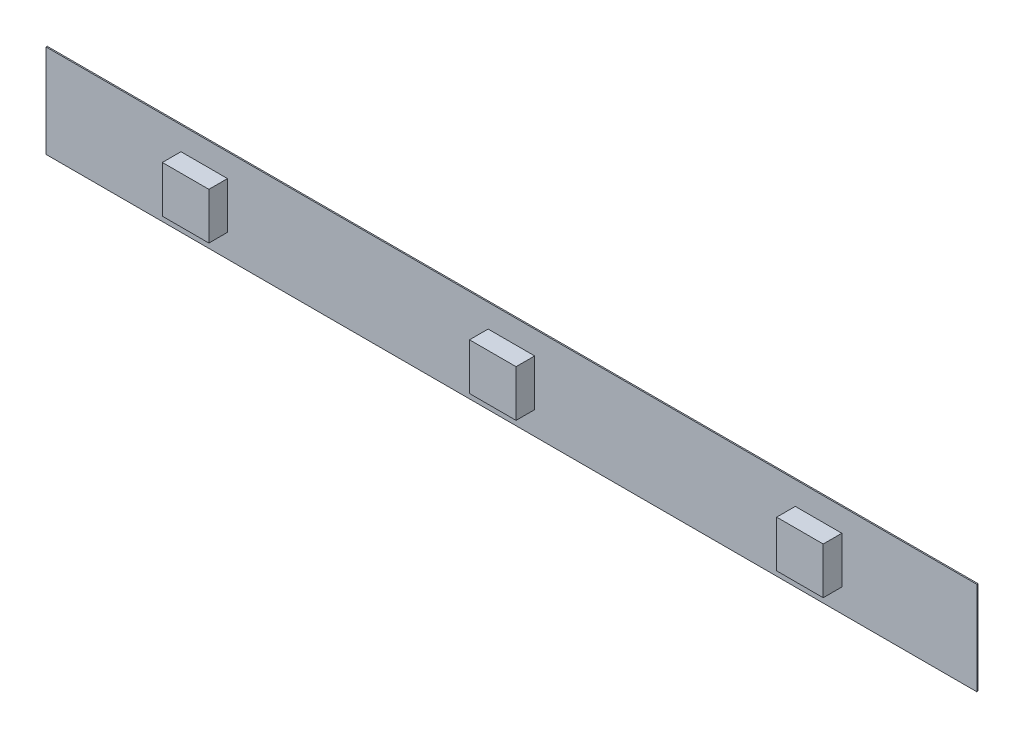
SolidWorks part; units mm, degrees
ref_plane "Alzado" through (0, 0, 0) normal (0, 0, 1) x (1, 0, 0)
ref_plane "Planta" through (0, 0, 0) normal (0, 1, 0) x (1, 0, 0)
ref_plane "Vista lateral" through (0, 0, 0) normal (1, 0, 0) x (0, 0, -1)
sketch "Croquis1" plane through (0, 0, 0) normal (0, 0, 1) x (1, 0, 0)
  line L1 (-54.4155, 5.8099) -> (45.5845, 5.8099)
  line L2 (-54.4155, 5.8099) -> (-54.4155, -4.1901)
  line L3 (-54.4155, -4.1901) -> (45.5845, -4.1901)
  line L4 (45.5845, 5.8099) -> (45.5845, -4.1901)
  line L5 (-39.9155, 3.3099) -> (-34.9155, 3.3099) construction
  line L6 (-39.9155, 3.3099) -> (-39.9155, -1.6901) construction
  line L7 (-39.9155, -1.6901) -> (-34.9155, -1.6901) construction
  line L8 (-34.9155, 3.3099) -> (-34.9155, -1.6901) construction
  line L9 (-6.9155, 3.3099) -> (-1.9155, 3.3099) construction
  line L10 (-6.9155, 3.3099) -> (-6.9155, -1.6901) construction
  line L11 (-6.9155, -1.6901) -> (-1.9155, -1.6901) construction
  line L12 (-1.9155, 3.3099) -> (-1.9155, -1.6901) construction
  line L13 (26.0845, 3.3099) -> (31.0845, 3.3099) construction
  line L14 (26.0845, 3.3099) -> (26.0845, -1.6901) construction
  line L15 (26.0845, -1.6901) -> (31.0845, -1.6901) construction
  line L16 (31.0845, 3.3099) -> (31.0845, -1.6901) construction
  dimension "D1" = 100
  dimension "D2" = 10
  dimension "D3" = 5
  dimension "D4" = 5
  dimension "D5" = 5
  dimension "D6" = 5
  dimension "D7" = 5
  dimension "D8" = 5
  dimension "D9" = 28
  dimension "D10" = 28
extrude "Saliente-Extruir1" add sketch "Croquis1" along normal blind 0.13
sketch "Croquis2" plane through (0, 0, 0.13) normal (0, 0, 1) x (1, 0, 0)
  line L0 (-4.4155, 3.3099) -> (-4.4155, -1.6901) construction
  line L1 (-39.9155, 3.3099) -> (-34.9155, 3.3099)
  line L2 (-39.9155, 3.3099) -> (-39.9155, -1.6901)
  line L3 (-39.9155, -1.6901) -> (-34.9155, -1.6901)
  line L4 (-34.9155, 3.3099) -> (-34.9155, -1.6901)
  line L5 (-6.9155, 3.3099) -> (-1.9155, 3.3099)
  line L6 (-6.9155, 3.3099) -> (-6.9155, -1.6901)
  line L7 (-6.9155, -1.6901) -> (-1.9155, -1.6901)
  line L8 (-1.9155, 3.3099) -> (-1.9155, -1.6901)
  line L9 (26.0845, 3.3099) -> (31.0845, 3.3099)
  line L10 (26.0845, 3.3099) -> (26.0845, -1.6901)
  line L11 (26.0845, -1.6901) -> (31.0845, -1.6901)
  line L12 (31.0845, 3.3099) -> (31.0845, -1.6901)
  line L13 (-4.4155, 5.8099) -> (-4.4155, -4.1901) construction
  line L14 (45.5845, 5.8099) -> (-54.4155, 5.8099) construction
  line L15 (-54.4155, -4.1901) -> (45.5845, -4.1901) construction
  dimension "D1" = 5
  dimension "D2" = 5
  dimension "D3" = 5
  dimension "D4" = 5
  dimension "D5" = 5
  dimension "D6" = 5
  dimension "D7" = 28
  dimension "D8" = 28
extrude "Saliente-Extruir2" add sketch "Croquis2" along normal blind 2
